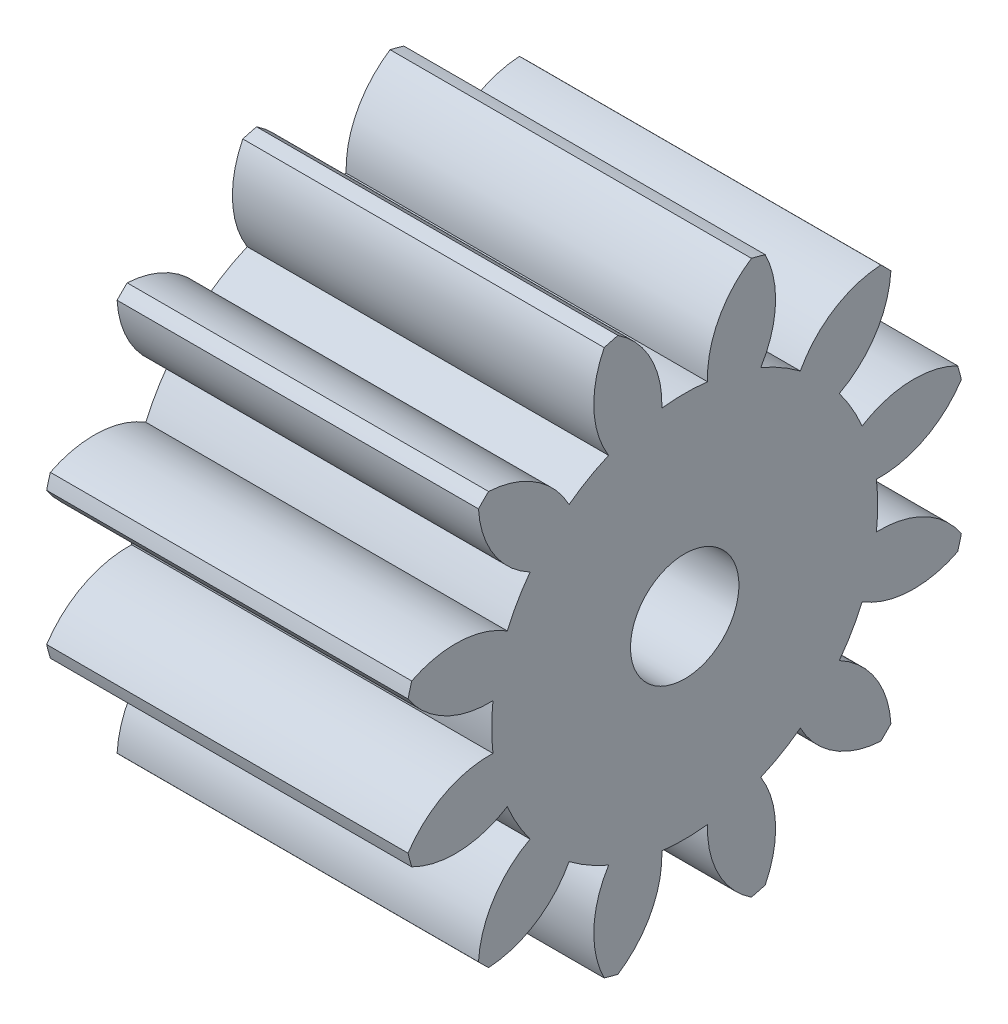
SolidWorks part; units mm, degrees
material "1060 Alloy"
ref_plane "Plane1" through (0, 0, 0) normal (0, 0, 1) x (1, 0, 0)
ref_plane "Plane2" through (0, 0, 0) normal (0, 1, 0) x (1, 0, 0)
ref_plane "Plane3" through (0, 0, 0) normal (1, 0, 0) x (0, 0, -1)
sketch "HoldingSke" plane through (0, 0, 0) normal (0, 1, 0) x (1, 0, 0)
  line L0 (0, 0) -> (0.8695, -0.1848)
  line L1 (-15, 0) -> (100, 0) construction
  line L2 (0, 0) -> (-2.1039, 2.3779)
  line L3 (0, 0) -> (-11.863, 4.5341)
  line L4 (0, 0) -> (8.4473, 1.7955)
  line L5 (0, 0) -> (-46.8476, -17.4728)
  line L6 (0, 0) -> (-8.2896, -5.593)
  line L7 (-2.1039, 2.3779) -> (8.6586, 51.2059)
  line L8 (-76.2, 54.61) -> (-75.7, 54.61)
  line L9 (-71.009, 38.7566) -> (-53.1078, 45.2721)
  line L10 (-76.2, 71.12) -> (104.1128, 71.12)
  line L11 (0, 0) -> (-10, 0)
  line L12 (-76.2, 101.6) -> (-76.158, 101.6)
  line L13 (24.9733, 27.94) -> (52.9518, 28.4284)
  line L14 (24.9733, 27.94) -> (24.9743, 27.94)
  line L15 (24.9733, 27.94) -> (100.4006, 29.5858)
  line L16 (-63.627, -1.125) -> (-12.827, -1.125)
  circle A0 centre (0, 0) radius 1.5
  circle A1 centre (0, 0) radius 5.3427
  circle A2 centre (0, 0) radius 37.5
  circle A3 centre (0, 0) radius 1.5
  dimension "MHD" = 10.6855
  dimension "Hub_dia" = 75
  dimension "Bore" = 3
  dimension "MBD" = 3
  dimension "Num_teeth" = 12
  dimension "Pitch_radius" = 180.3128
  dimension "Pitch" = 0.8889
  dimension "Width" = 10
  dimension "Overall_len" = 50
  dimension "Show_teeth" = 12
  dimension "Thickness" = 10
  dimension "OAL" = 50.0001
  dimension "T_dim" = 0.5
  dimension "Ap" = 20
  dimension "H" = 19.05
  dimension "Backlash" = 0.042
  dimension "Addendum_fac" = 1
  dimension "Dedendum_fac" = 1.25
  dimension "Clearance_fac" = 0.25
  dimension "Dedendum_add" = 0.001
  dimension "Module" = 1.125
sketch "BasProSke" plane through (0, 0, 0) normal (0, 1, 0) x (1, 0, 0)
  line L0 (-10, 0) -> (60, 0) construction
  line L1 (0, 0) -> (0, 7.875)
  line L2 (0, 0) -> (10, 0)
  line L3 (10, 0) -> (10, 7.875)
  line L4 (10, 7.875) -> (0, 7.875)
  dimension "Diameter" = 15.75
  dimension "Thickness" = 10
revolve "Base-Revolve" add sketch "BasProSke" angle 360 about L0
sketch "TooCutSke" plane through (0, 0, 0) normal (1, 0, 0) x (0, 0, -1)
  line L1 (0, 0) -> (0, 107) construction
  line L2 (0, 0) -> (-0.9544, 6.6822) construction
  line L3 (0, 0) -> (-3.469, 12.9463) construction
  line L4 (-0.9544, 6.6822) -> (-1.7345, 6.4732) construction
  arc A0 (0.6314, 5.3053) -> (-0.6314, 5.3053) centre (0, 0) ccw
  arc A1 (1.8767, 7.6743) -> (-1.8767, 7.6743) centre (0, 0) ccw
  circle A2 centre (0, 0) radius 6.75 construction
  circle A3 centre (0, 0) radius 6.3429 construction
  arc A4 (-0.6314, 5.3053) -> (-1.8767, 7.6743) centre (-3.3298, 5.3986) ccw
  arc A5 (1.8767, 7.6743) -> (0.6314, 5.3053) centre (3.3298, 5.3986) ccw
  dimension "Root_dia" = 10.6855
  dimension "Overcut_dia" = 15.8008
  dimension "Pitch_dia" = 13.5
  dimension "Base_dia" = 12.6859
  dimension "Flank_rad" = 2.7
  dimension "Half_ang" = 15
  dimension "Half_CT" = 0.8076
extrude "ToothCut" cut sketch "TooCutSke" along normal through all
fillet "Breaks" [suppressed] radius 0.0225
fillet "RootFillets" [suppressed] radius 0.2823
pattern_circular "TeethCuts" count 12 every 30 about axis through (-10, 0, 0) along (1, 0, 0) of "ToothCut", "RootFillets", "Breaks"
sketch "HubNeaOneSke" plane through (0, 0, 0) normal (-1, 0, 0) x (0, 0, 1)
  circle A0 centre (0, 0) radius 5.3427
  dimension "Diameter" = 10.6855
extrude "HubNearOne" [suppressed] add sketch "HubNeaOneSke" along normal blind 40.0001
sketch "HubNeaBotSke" plane through (0, 0, 0) normal (-1, 0, 0) x (0, 0, 1)
  circle A0 centre (0, 0) radius 5.3427
  dimension "Diameter" = 10.6855
extrude "HubNearBoth" [suppressed] add sketch "HubNeaBotSke" along normal blind 20
ref_plane "FarPln" through (10, 0, 0) normal (1, 0, 0) x (0, 0, -1)
sketch "HubFarSke" plane through (10, 0, 0) normal (1, 0, 0) x (0, 0, -1)
  circle A0 centre (0, 0) radius 5.3427
  dimension "Diameter" = 10.6855
extrude "HubFar" [suppressed] add sketch "HubFarSke" along normal blind 20
sketch "BorSke" plane through (0, 0, 0) normal (1, 0, 0) x (0, 0, -1)
  circle A0 centre (0, 0) radius 1.5
  dimension "Diameter" = 3
extrude "Bore" cut sketch "BorSke" along normal mid plane 100.0001
sketch "KeySke" plane through (0, 0, 0) normal (1, 0, 0) x (0, 0, -1)
  line L0 (-0.6, 0) -> (-0.6, 2)
  line L1 (-0.6, 2) -> (0.6, 2)
  line L2 (0.6, 2) -> (0.6, 0)
  line L3 (0, 0) -> (0, 34) construction
  line L4 (-0.6, 0) -> (0.6, 0)
  dimension "Offset" = 2
  dimension "Width" = 1.2
extrude "Keyway" [suppressed] cut sketch "KeySke" along normal mid plane 100.0001
pattern_circular "Keyway2" [suppressed] count 2 every 90 about axis through (-10, 0, 0) along (1, 0, 0)
equation "' \"Module@HoldingSke\" = 6.35"
equation "' \"Num_teeth@HoldingSke\" = 12"
equation "' \"Ap@HoldingSke\" =  20"
equation "' \"Width@HoldingSke\" = 0.5 * 25.4"
equation "' \"Hub_dia@HoldingSke\"= 1 * 25.4"
equation "' \"Overall_len@HoldingSke\" = 1.0 * 25.4"
equation "' \"Bore@HoldingSke\" = 0.75 * 25.4"
equation "' \"T_dim@HoldingSke\" = 0.1 * 25.4"
equation "' \"Width@KeySke\" = 0.25 * 25.4"
equation "' \"Show_teeth@HoldingSke\" = 13"
equation "' \"Backlash@HoldingSke\" = 0.009 * 25.4"
equation "' \"Addendum_fac@HoldingSke\" = 1.0"
equation "' \"Dedendum_fac@HoldingSke\" = 1.25"
equation "' \"Dedendum_add@HoldingSke\" = 0.00005 * 25.4"
equation "' \"Clearance_fac@HoldingSke\" = 0.25"
equation "\"Pitch@HoldingSke\" = 1 / \"Module@HoldingSke\""
equation "\"Overcut_dia@TooCutSke\" = (\"Num_teeth@HoldingSke\" + 2 * \"Addendum_fac@HoldingSke\") / \"Pitch@HoldingSke\" + 0.002 * 25.4"
equation "\"Pitch_dia@TooCutSke\" = \"Num_teeth@HoldingSke\" / \"Pitch@HoldingSke\""
equation "\"Base_dia@TooCutSke\" = \"Num_teeth@HoldingSke\" / \"Pitch@HoldingSke\" * cos((\"Ap@HoldingSke\"  * 3.14159265 / 180))"
equation "\"Root_dia@TooCutSke\" = (\"Num_teeth@HoldingSke\" + 2) / \"Pitch@HoldingSke\" - 2 * (\"Addendum_fac@HoldingSke\" + \"Dedendum_fac@HoldingSke\") / \"Pitch@HoldingSke\" - \"Dedendum_add@HoldingSke\" * 2"
equation "\"Half_ang@TooCutSke\" = 180 / \"Num_teeth@HoldingSke\""
equation "\"Half_CT@TooCutSke\" = \"Num_teeth@HoldingSke\" / \"Pitch@HoldingSke\" * sin((3.14159265 / 2 / \"Num_teeth@HoldingSke\")) / 2 - 7 * \"Backlash@HoldingSke\" / 4"
equation "\"Flank_rad@TooCutSke\" = \"Num_teeth@HoldingSke\" / \"Pitch@HoldingSke\" / 5"
equation "\"Radius@RootFillets\" = \"Clearance_fac@HoldingSke\" / \"Pitch@HoldingSke\" + \"Dedendum_add@HoldingSke\""
equation "\"Break_rad@Breaks\" = 0.02 / \"Pitch@HoldingSke\""
equation "\"Thickness@HoldingSke\" = \"Width@HoldingSke\""
equation "\"OAL@HoldingSke\" = \"Thickness@HoldingSke\""
equation "\"MHD@HoldingSke\" = (\"Num_teeth@HoldingSke\" + 2) / \"Pitch@HoldingSke\" - 2 * (\"Addendum_fac@HoldingSke\" + \"Dedendum_fac@HoldingSke\")  / \"Pitch@HoldingSke\" - \"Dedendum_add@HoldingSke\" * 2"
equation "\"MBD@HoldingSke\" = (\"Num_teeth@HoldingSke\" + 2) / \"Pitch@HoldingSke\" - 2 * (\"Addendum_fac@HoldingSke\" + \"Dedendum_fac@HoldingSke\")  / \"Pitch@HoldingSke\" - \"Dedendum_add@HoldingSke\" * 2 - 0.002 * 25.4"
equation "\"MHD@HoldingSke\" = ((sgn( \"MHD@HoldingSke\" - \"Hub_dia@HoldingSke\" )-1)*( \"MHD@HoldingSke\" - \"Hub_dia@HoldingSke\" ))/-2+ \"Hub_dia@HoldingSke\""
equation "\"MBD@HoldingSke\" = ((sgn( \"MBD@HoldingSke\" - \"Bore@HoldingSke\" )-1)*( \"MBD@HoldingSke\" - \"Bore@HoldingSke\" ))/-2+ \"Bore@HoldingSke\""
equation "\"OAL@HoldingSke\" = ((sgn( \"OAL@HoldingSke\" - \"Overall_len@HoldingSke\" )+1)*( \"OAL@HoldingSke\" - \"Overall_len@HoldingSke\" ))/2 + \"Overall_len@HoldingSke\" + 0.000002 * 25.4"
equation "\"Num_teeth@TeethCuts\" = int( \"Show_teeth@HoldingSke\" ) + 1"
equation "\"Num_teeth@TeethCuts\" = ((sgn( \"Num_teeth@TeethCuts\" - \"Num_teeth@HoldingSke\" )-1)*( \"Num_teeth@TeethCuts\" - \"Num_teeth@HoldingSke\" ))/-2+ \"Num_teeth@HoldingSke\""
equation "\"Num_teeth@TeethCuts\" = ((sgn( \"Num_teeth@TeethCuts\" - 2.0)+1)*( \"Num_teeth@TeethCuts\" - 2.0))/2 +2.0"
equation "\"Angle@TeethCuts\" = 360.0 / \"Num_teeth@HoldingSke\""
equation "\"Diameter@BasProSke\" = (\"Num_teeth@HoldingSke\" + 2 * \"Addendum_fac@HoldingSke\") / \"Pitch@HoldingSke\""
equation "\"Thickness@BasProSke\"  = \"Thickness@HoldingSke\""
equation "' \"Fillet_rad@BasProSke\" =  \"Thickness@HoldingSke\" * 0.05"
equation "\"MHD@HoldingSke\" = ((sgn( \"MHD@HoldingSke\" - \"Root_dia@TooCutSke\" )-1)*( \"MHD@HoldingSke\" - \"Root_dia@TooCutSke\" ))/-2+ \"Root_dia@TooCutSke\""
equation "\"Diameter@HubNeaOneSke\" = \"MHD@HoldingSke\""
equation "\"Length@HubNearOne\" = \"OAL@HoldingSke\" - \"Thickness@BasProSke\""
equation "\"Diameter@HubNeaBotSke\" = \"MHD@HoldingSke\""
equation "\"Length@HubNearBoth\" = ( \"OAL@HoldingSke\" - \"Thickness@BasProSke\" ) / 2.0"
equation "\"Thickness@FarPln\" = \"Thickness@BasProSke\""
equation "\"Diameter@HubFarSke\" = \"MHD@HoldingSke\""
equation "\"Length@HubFar\" = ( \"OAL@HoldingSke\" - \"Thickness@BasProSke\" ) / 2.0"
equation "\"Diameter@BorSke\" = \"MBD@HoldingSke\""
equation "\"D1@Bore\" = \"OAL@HoldingSke\" * 2.0"
equation "\"D1@Keyway\" = \"OAL@HoldingSke\" * 2.0"
equation "\"Offset@KeySke\" = \"T_dim@HoldingSke\" + \"MBD@HoldingSke\" / 2.0"
